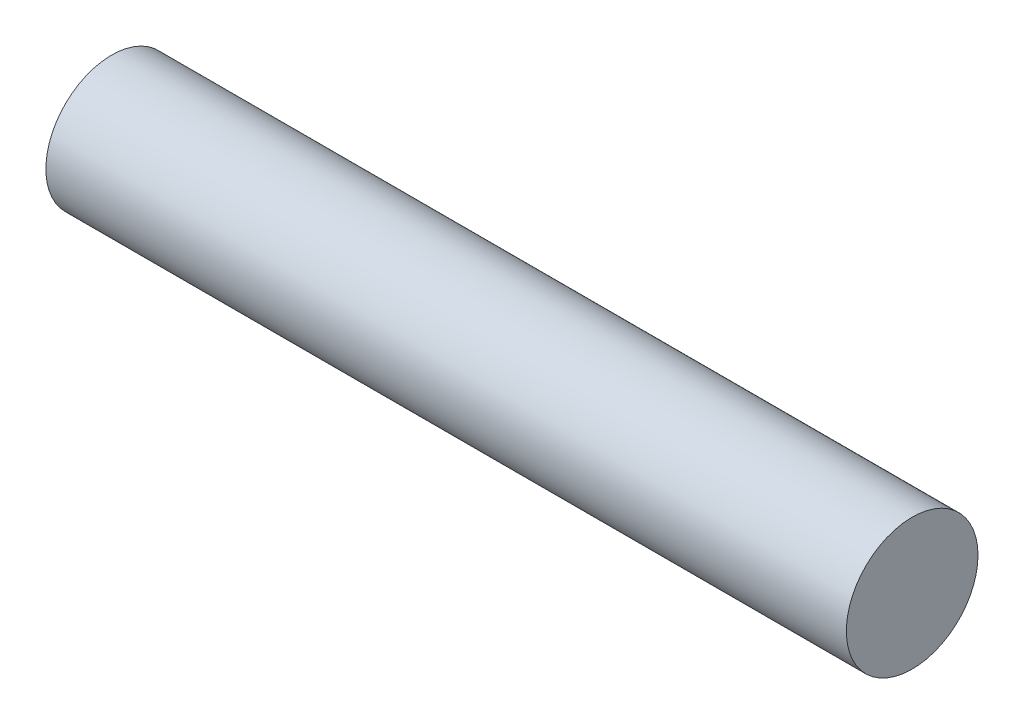
SolidWorks part; units mm, degrees
ref_plane "Front Plane" through (0, 0, 0) normal (1, 0, 0) x (0, 1, 0)
ref_plane "Top Plane" through (0, 0, 0) normal (0, 0, 1) x (0, 1, 0)
ref_plane "Right Plane" through (0, 0, 0) normal (0, 1, 0) x (-1, 0, 0)
sketch "Sketch1" plane through (0, 0, 0) normal (1, 0, 0) x (0, 1, 0)
  circle A0 centre (0, 0) radius 2.5
  dimension "D1" = 5
extrude "Boss-Extrude1" add sketch "Sketch1" along normal blind 30.4
